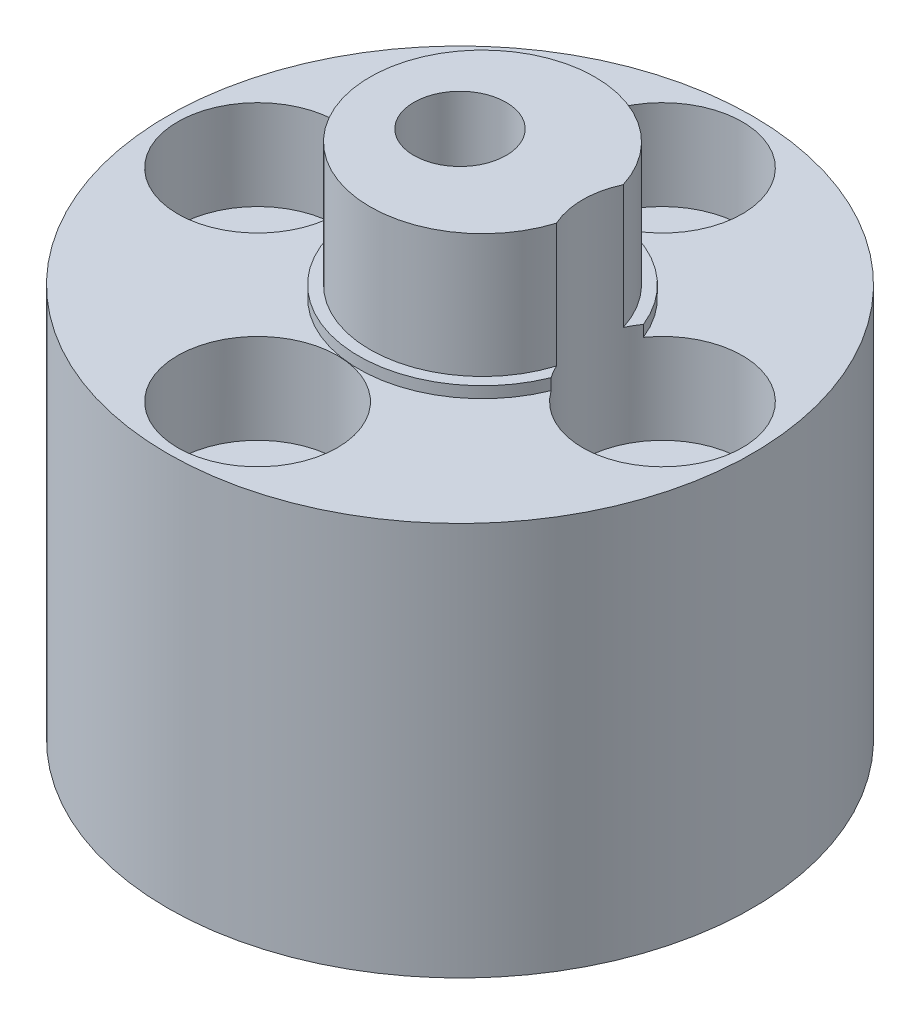
SolidWorks part; units mm, degrees
ref_plane "Front Plane" through (0, 0, 0) normal (0, 0, 1) x (1, 0, 0)
ref_plane "Top Plane" through (0, 0, 0) normal (0, 1, 0) x (1, 0, 0)
ref_plane "Right Plane" through (0, 0, 0) normal (1, 0, 0) x (0, 0, -1)
sketch "Sketch1" plane through (0, 0, 0) normal (0, 1, 0) x (1, 0, 0)
  circle A0 centre (0, 0) radius 13
  dimension "D1" = 26
extrude "Boss-Extrude1" add sketch "Sketch1" along normal blind 17.5
sketch "Sketch6" plane through (0, 17.5, 0) normal (0, 1, 0) x (1, 0, 0)
  circle A0 centre (1, 0) radius 5
  dimension "D2" = 10
  dimension "D1" = 1
extrude "Boss-Extrude2" add sketch "Sketch6" along normal blind 6
sketch "Sketch7" plane through (0, 17.5, 0) normal (0, 1, 0) x (1, 0, 0)
  circle A0 centre (1, 0) radius 5.5
  dimension "D1" = 11
extrude "Boss-Extrude3" add sketch "Sketch7" along normal blind 0.5
sketch "Sketch2" plane through (0, 0, 0) normal (0, 1, 0) x (1, 0, 0)
  line L0 (0, 9) -> (0, 0) construction
  line L1 (0, 0) -> (4.2426, 4.2426) construction
  circle A0 centre (0, 9) radius 1.65
  circle A1 centre (4.2426, 4.2426) radius 1.65 construction
  dimension "D1" = 3.3
  dimension "D2" = 3.3
  dimension "D4" = 6
  dimension "D3" = 9
  dimension "D5" = 45
extrude "Cut-Extrude1" cut sketch "Sketch2" along normal through all
sketch "Sketch5" plane through (0, 17.5, 0) normal (0, 1, 0) x (1, 0, 0)
  circle A0 centre (0, 9) radius 3.55
  dimension "D1" = 7.1
extrude "Cut-Extrude3" cut sketch "Sketch5" against normal blind 4 and the other way through all
pattern_circular "CirPattern1" count 4 over 360 about axis through (0, 0, 0) along (0, 1, 0) of "Cut-Extrude1", "Cut-Extrude3"
sketch "Sketch3" plane through (0, 0, 0) normal (0, 1, 0) x (1, 0, 0)
  circle A0 centre (0, 0) radius 2.05
  dimension "D1" = 4.1
extrude "Cut-Extrude2" cut sketch "Sketch3" along normal through all
sketch "Sketch8" plane through (0, 0, 0) normal (0, -1, 0) x (1, 0, 0)
  circle A0 centre (0, 0) radius 2.75
  dimension "D1" = 5.5
extrude "Cut-Extrude4" cut sketch "Sketch8" against normal blind 10
sketch "Sketch10" plane through (0, 0, 0) normal (0, -1, 0) x (1, 0, 0)
  line L1 (4.6188, 0) -> (2.3094, 4)
  line L2 (2.3094, 4) -> (-2.3094, 4)
  line L3 (-2.3094, 4) -> (-4.6188, 0)
  line L4 (-4.6188, 0) -> (-2.3094, -4)
  line L5 (-2.3094, -4) -> (2.3094, -4)
  line L6 (2.3094, -4) -> (4.6188, 0)
  circle A0 centre (0, 0) radius 4 construction
  dimension "D1" = 8
extrude "Cut-Extrude5" cut sketch "Sketch10" against normal up to surface (10 mm away) contours L1 L2 L3 L4 L5 L6 up to face at (0, 10, -2.05)
